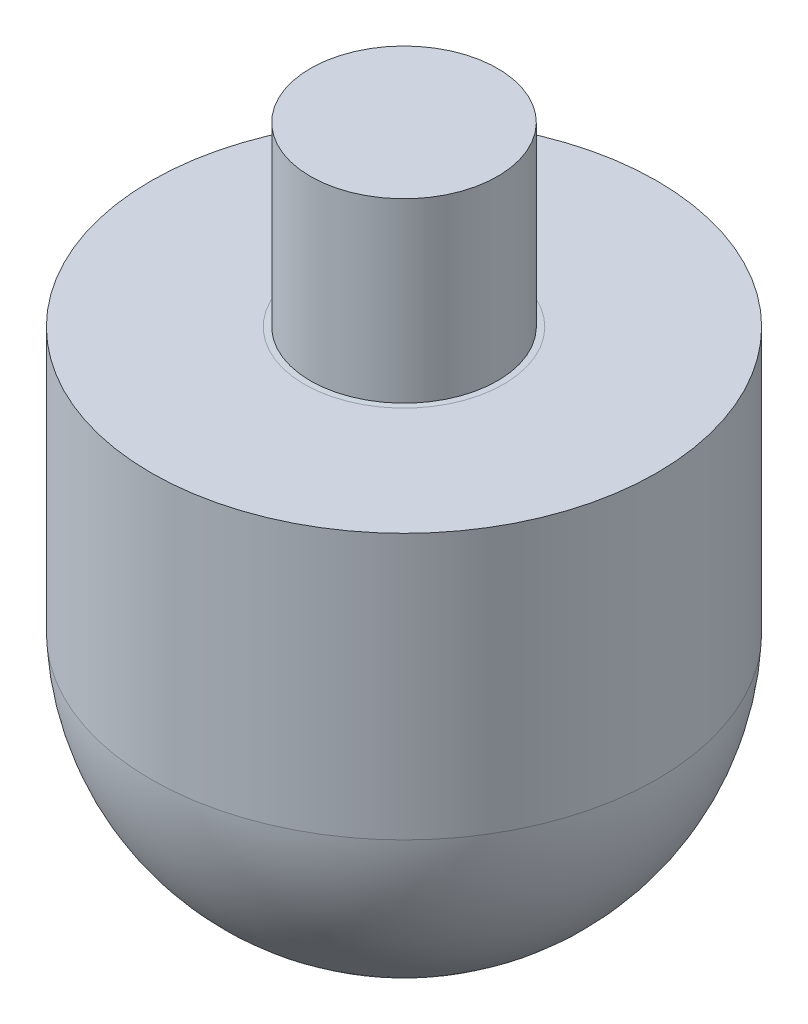
SolidWorks part; units mm, degrees
ref_plane "Front Plane" through (0, 0, 0) normal (0, 0, 1) x (1, 0, 0)
ref_plane "Top Plane" through (0, 0, 0) normal (0, 1, 0) x (1, 0, 0)
ref_plane "Right Plane" through (0, 0, 0) normal (1, 0, 0) x (0, 0, -1)
sketch "Sketch1" plane through (0, 0, 0) normal (0, 0, 1) x (1, 0, 0)
  line L0 (0, 38.7187) -> (0, -37.4062) construction
  line L1 (-50.0625, 0) -> (58.6875, 0) construction
  line L2 (0, 25.0001) -> (0, -13.6448)
  line L3 (14.2859, 0) -> (14.2859, 14.9978)
  line L4 (14.2859, 14.9978) -> (5.625, 14.9978)
  line L5 (5.2859, 15.0001) -> (5.2859, 25.0001)
  line L6 (5.2859, 25.0001) -> (0, 25.0001)
  line L7 (5.2859, 15.0001) -> (5.625, 14.9978)
  arc A0 (0, -13.6448) -> (14.2859, 0) centre (0, 0.6563) ccw
  dimension "D3" = 10
  dimension "D4" = 9
  dimension "D5" = 5.2859
revolve "Revolve1" add sketch "Sketch1" angle 360 about L2
